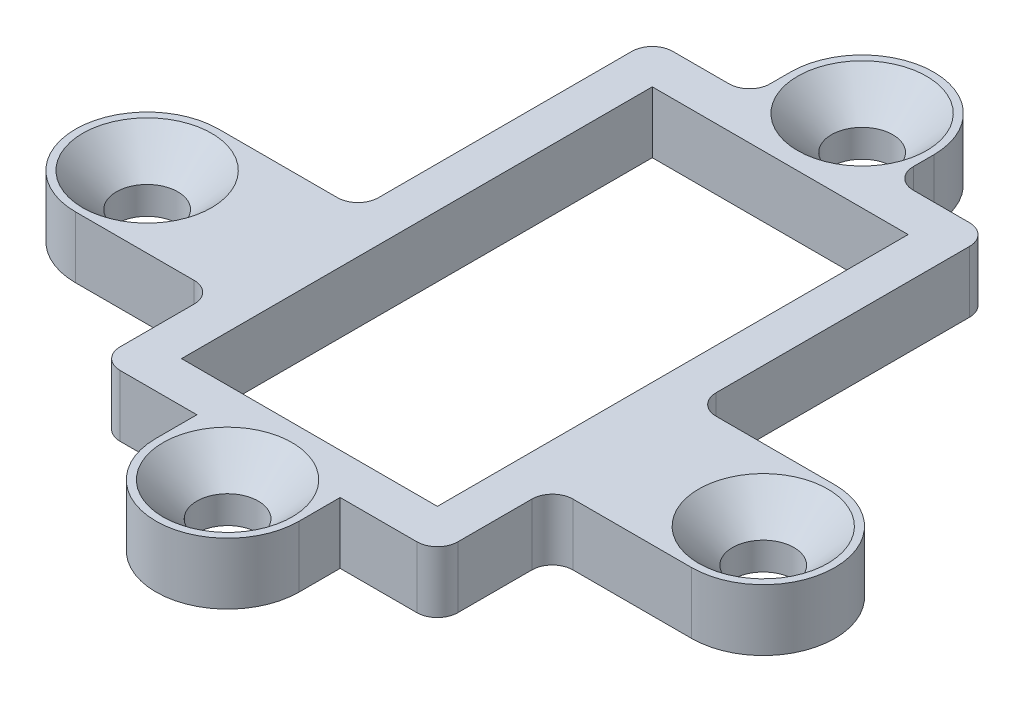
SolidWorks part; units mm, degrees
ref_plane "Front Plane" through (0, 0, 0) normal (0, 0, 1) x (1, 0, 0)
ref_plane "Top Plane" through (0, 0, 0) normal (0, 1, 0) x (1, 0, 0)
ref_plane "Right Plane" through (0, 0, 0) normal (1, 0, 0) x (0, 0, -1)
sketch "Sketch1" plane through (0, 0, 0) normal (0, 1, 0) x (1, 0, 0)
  line L0 (-15.05, 0) -> (0, 0) construction
  line L1 (0, 0) -> (15.05, 0) construction
  line L2 (0, 19.88) -> (0, 0) construction
  line L3 (0, 0) -> (0, -11.12) construction
  line L4 (-8.25, 17.88) -> (8.25, 17.88)
  line L5 (-6.25, 15.88) -> (6.25, 15.88)
  line L6 (-6.25, 15.88) -> (-6.25, -7.12)
  line L7 (-6.25, -7.12) -> (6.25, -7.12)
  line L8 (6.25, 15.88) -> (6.25, -7.12)
  line L9 (-6.25, 15.88) -> (6.25, -7.12) construction
  line L10 (-6.25, -7.12) -> (6.25, 15.88) construction
  line L11 (8.25, 17.88) -> (8.25, -9.12)
  line L12 (-8.25, -9.12) -> (8.25, -9.12)
  line L13 (-8.25, 17.88) -> (-8.25, -9.12)
  line L14 (-3.5, 19.88) -> (-3.5, 17.88)
  line L15 (3.5, 19.88) -> (3.5, 17.88)
  line L16 (3.5, -11.12) -> (3.5, -9.12)
  line L17 (-3.5, -11.12) -> (-3.5, -9.12)
  line L18 (-15.05, 3.5) -> (-8.25, 3.5)
  line L19 (-15.05, -3.5) -> (-8.25, -3.5)
  line L20 (15.05, 3.5) -> (8.25, 3.5)
  line L21 (15.05, -3.5) -> (8.25, -3.5)
  circle A4 centre (0, 19.88) radius 3.5
  circle A5 centre (0, -11.12) radius 3.5
  circle A6 centre (15.05, 0) radius 3.5
  circle A7 centre (-15.05, 0) radius 3.5
  point P18 (0, 4.38)
  dimension "D4" = 19.88
  dimension "D7" = 4
  dimension "D8" = 4
  dimension "D9" = 12.5
  dimension "D10" = 2
extrude "Boss-Extrude1" add sketch "Sketch1" along normal blind 3
fillet "Fillet1" radius 1 10 edges at (-8.25, 1.5, -3.5) (-8.25, 1.5, 3.5) (-8.25, 1.5, 9.12) (8.25, 1.5, 9.12) (8.25, 1.5, 3.5) (8.25, 1.5, -3.5) (8.25, 1.5, -17.88) (3.5, 1.5, -17.88) (-3.5, 1.5, -17.88) (-8.25, 1.5, -17.88)
hole_wizard "CSK for M3 Flat Head Machine Screw2" positions "Sketch3" profile "Sketch2" countersink size "M3" standard "ANSI Metric" end condition through all
sketch "Sketch3" plane through (0, 3, 0) normal (0, 1, 0) x (1, 0, 0)
  point P0 (15.05, 0)
  point P3 (-15.05, 0)
  point P6 (0, -11.12)
  point P9 (0, 19.88)
sketch "Sketch2" plane through (15.05, 3, 0) normal (1, 0, 0) x (0, 0, 1)
  line L0 (0, 0) -> (0, 3)
  line L1 (0, 3) -> (1.5, 3)
  line L2 (1.5, 3) -> (1.5, 1.65)
  line L3 (1.5, 1.65) -> (3.15, 0)
  line L5 (3.15, 0) -> (0, 0)
  line L6 (-1.5, 1.65) -> (-3.15, 0) construction
  line L11 (0, -6.35) -> (0, 107.95) construction
  dimension "Thru Hole Dia." = 3
  dimension "Thru Hole Depth" = 3
  dimension "Near C'Sink Dia." = 6.3
  dimension "Near C'Sink Angle" = 90
